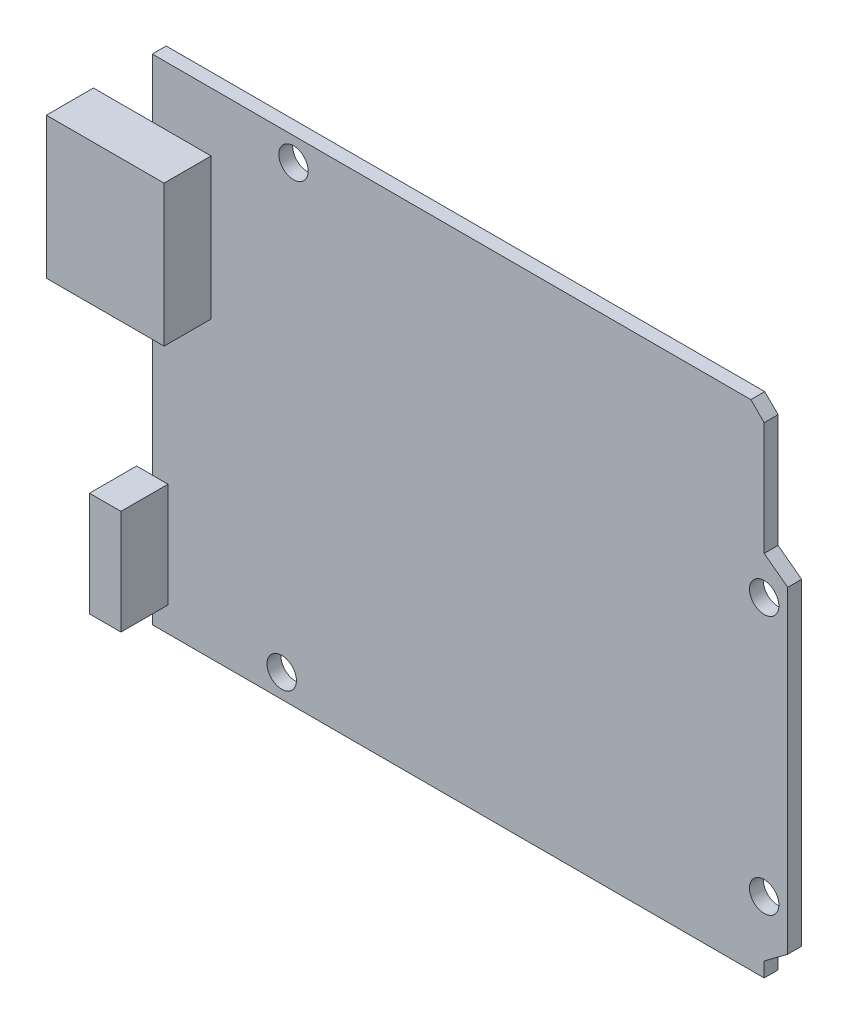
SolidWorks part; units mm, degrees
ref_plane "Front Plane" through (0, 0, 0) normal (0, 0, 1) x (1, 0, 0)
ref_plane "Top Plane" through (0, 0, 0) normal (0, 1, 0) x (1, 0, 0)
ref_plane "Right Plane" through (0, 0, 0) normal (1, 0, 0) x (0, 0, -1)
sketch "Sketch1" plane through (0, 0, 0) normal (0, 0, 1) x (1, 0, 0)
  line L1 (-34.29, -26.67) -> (34.29, -26.67)
  line L2 (-34.29, -26.67) -> (-34.29, 26.67)
  line L3 (-34.29, 26.67) -> (34.29, 26.67)
  line L4 (34.29, -26.67) -> (34.29, 26.67)
  line L5 (-34.29, -26.67) -> (34.29, 26.67) construction
  line L6 (-34.29, 26.67) -> (34.29, -26.67) construction
  point P0 (0, 0)
  dimension "D1" = 68.58
  dimension "D2" = 53.34
extrude "Boss-Extrude1" add sketch "Sketch1" along normal blind 1.5
sketch "Sketch2" plane through (0, 0, 1.5) normal (0, 0, 1) x (1, 0, 0)
  line L0 (-34.29, 26.67) -> (-34.29, -26.67) construction
  line L1 (-40.64, 5.08) -> (-27.94, 5.08)
  line L2 (-40.64, 5.08) -> (-40.64, 20.32)
  line L3 (-40.64, 20.32) -> (-27.94, 20.32)
  line L4 (-27.94, 5.08) -> (-27.94, 20.32)
  line L5 (-40.64, 5.08) -> (-27.94, 20.32) construction
  line L6 (-40.64, 20.32) -> (-27.94, 5.08) construction
  line L7 (34.29, 26.67) -> (-34.29, 26.67) construction
  line L9 (-35.9875, -23.9716) -> (-32.5925, -23.9716)
  line L10 (-35.9875, -23.9716) -> (-35.9875, -12.686)
  line L11 (-35.9875, -12.686) -> (-32.5925, -12.686)
  line L12 (-32.5925, -23.9716) -> (-32.5925, -12.686)
  line L13 (-35.9875, -23.9716) -> (-32.5925, -12.686) construction
  line L14 (-35.9875, -12.686) -> (-32.5925, -23.9716) construction
  point P0 (-34.29, 12.7)
  point P9 (-34.29, -18.3288)
  dimension "D1" = 12.7
  dimension "D2" = 15.24
  dimension "D3" = 6.35
extrude "Boss-Extrude2" add sketch "Sketch2" along normal blind 5.08
sketch "Sketch3" plane through (0, 0, 1.5) normal (0, 0, 1) x (1, 0, 0)
  line L0 (-34.29, -26.67) -> (34.29, -26.67) construction
  line L1 (-34.29, 5.08) -> (-34.29, -12.686) construction
  circle A0 centre (-19.05, 24.13) radius 1.5875
  circle A1 centre (-20.32, -24.13) radius 1.5875
  circle A2 centre (31.75, 8.89) radius 1.5875
  circle A3 centre (31.75, -19.05) radius 1.5875
  dimension "D1" = 3.175
  dimension "D2" = 1.27
  dimension "D3" = 50.8
  dimension "D4" = 5.08
  dimension "D5" = 2.54
  dimension "D6" = 27.94
  dimension "D7" = 15.24
  dimension "D8" = 13.97
extrude "Cut-Extrude1" cut sketch "Sketch3" against normal blind 10.16
sketch "Sketch4" plane through (0, 0, 1.5) normal (0, 0, 1) x (1, 0, 0)
  line L0 (30.3132, 26.67) -> (31.75, 25.2332)
  line L1 (34.29, 26.67) -> (-34.29, 26.67) construction
  line L3 (31.75, 13.0127) -> (34.29, 11.1158)
  line L4 (34.29, -26.67) -> (34.29, 26.67) construction
  line L5 (34.29, 11.1158) -> (34.29, 26.67)
  line L6 (34.29, 26.67) -> (30.3132, 26.67)
  line L7 (34.29, -23.1815) -> (31.75, -25.0785)
  line L8 (31.75, 13.0127) -> (31.75, 25.2332)
  line L9 (31.75, -25.0785) -> (31.75, -26.67)
  line L10 (-34.29, -26.67) -> (34.29, -26.67) construction
  line L11 (31.75, -26.67) -> (34.29, -26.67)
  line L12 (34.29, -26.67) -> (34.29, -23.1815)
  point P18 (33.02, -24.13)
  dimension "D1" = 45
  dimension "D2" = 2.032
  dimension "D3" = 2.54
extrude "Cut-Extrude2" cut sketch "Sketch4" against normal through all
